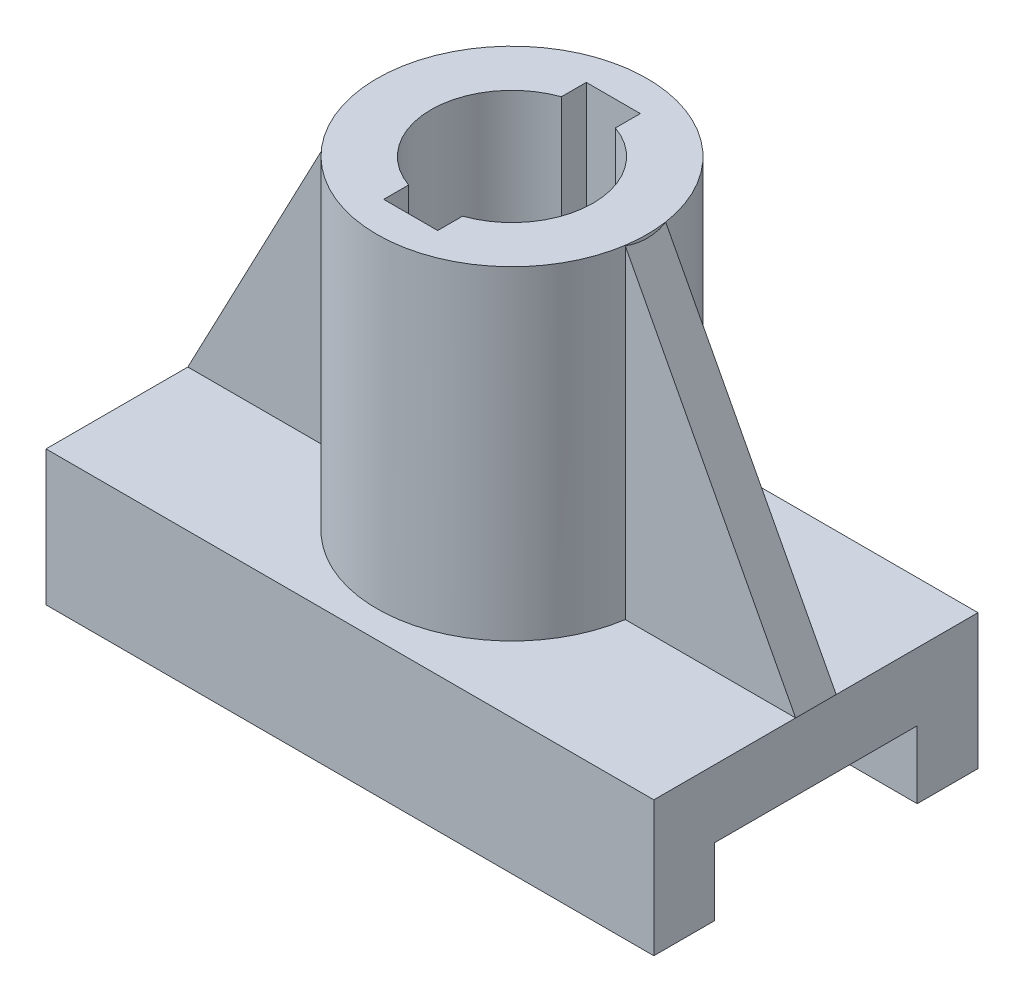
SolidWorks part; units mm, degrees
ref_plane "Front Plane" through (0, 0, 0) normal (0, 0, 1) x (1, 0, 0)
ref_plane "Top Plane" through (0, 0, 0) normal (0, 1, 0) x (1, 0, 0)
ref_plane "Right Plane" through (0, 0, 0) normal (1, 0, 0) x (0, 0, -1)
sketch "Sketch1" plane through (0, 0, 0) normal (0, 1, 0) x (1, 0, 0)
  line L1 (-45, 24) -> (45, 24)
  line L2 (-45, 24) -> (-45, -24)
  line L3 (-45, -24) -> (45, -24)
  line L4 (45, 24) -> (45, -24)
  line L5 (-45, 24) -> (45, -24) construction
  line L6 (-45, -24) -> (45, 24) construction
  point P0 (0, 0)
  dimension "D1" = 90
  dimension "D2" = 48
extrude "Boss-Extrude1" add sketch "Sketch1" along normal blind 20
sketch "Sketch2" plane through (0, 20, 0) normal (0, 1, 0) x (1, 0, 0)
  circle A0 centre (0, 0) radius 20
extrude "Boss-Extrude2" add sketch "Sketch2" along normal blind 48
sketch "Sketch3" plane through (0, 68, 0) normal (0, 1, 0) x (1, 0, 0)
  circle A0 centre (0, 0) radius 12
  circle A1 centre (0, 0) radius 20 construction
  dimension "D1" = 24
extrude "Cut-Extrude1" cut sketch "Sketch3" against normal blind 48
sketch "Sketch4" plane through (0, 68, 0) normal (0, 1, 0) x (1, 0, 0)
  line L1 (-4, -15) -> (4, -15)
  line L2 (-4, -15) -> (-4, 15)
  line L3 (-4, 15) -> (4, 15)
  line L4 (4, -15) -> (4, 15)
  line L5 (-4, -15) -> (4, 15) construction
  line L6 (-4, 15) -> (4, -15) construction
  point P0 (0, 0)
  dimension "D1" = 8
  dimension "D2" = 30
extrude "Cut-Extrude2" cut sketch "Sketch4" against normal blind 48
sketch "Sketch5" plane through (-45, 0, 0) normal (-1, 0, 0) x (0, 0, 1)
  line L0 (-24, 0) -> (24, 0) construction
  line L1 (-15, 0) -> (15, 0)
  line L2 (-15, 0) -> (-15, 10)
  line L3 (-15, 10) -> (15, 10)
  line L4 (15, 0) -> (15, 10)
  point P6 (0, 0)
  dimension "D1" = 10
  dimension "D2" = 30
  dimension "D3" = 9
extrude "Cut-Extrude4" cut sketch "Sketch5" along normal through all and the other way through all
sketch "Sketch7" plane through (0, 0, 0) normal (0, 0, 1) x (1, 0, 0)
  line L0 (20, 67.5) -> (45, 20)
  line L1 (20, 20) -> (20, 68) construction
  point P5 (0, 0)
  point P6 (0, 0)
  point P7 (0, 0)
  point P8 (0, 0)
  point P10 (0, 0)
  point P11 (20, 66.8236)
  point P12 (20, 67.4118)
  point P13 (0, 0)
  point P14 (0, 0)
  point P15 (0, 0)
  point P16 (0, 0)
  point P17 (20, 44)
  point P18 (0, 0)
  point P19 (20, 44)
  point P20 (0, 0)
  point P21 (0, 0)
  point P22 (0, 0)
  point P23 (0, 0)
  point P24 (0, 0)
  point P25 (0, 0)
  dimension "D1" = 67.5
rib "Rib5" sketch "Sketch7" sketch "Sketch7" thickness 6 extrusion direction parallel to sketch draft on no parameters "D1"=6
mirror "Mirror1" about plane through (0, 0, 0) normal (1, 0, 0) of bodies 105
